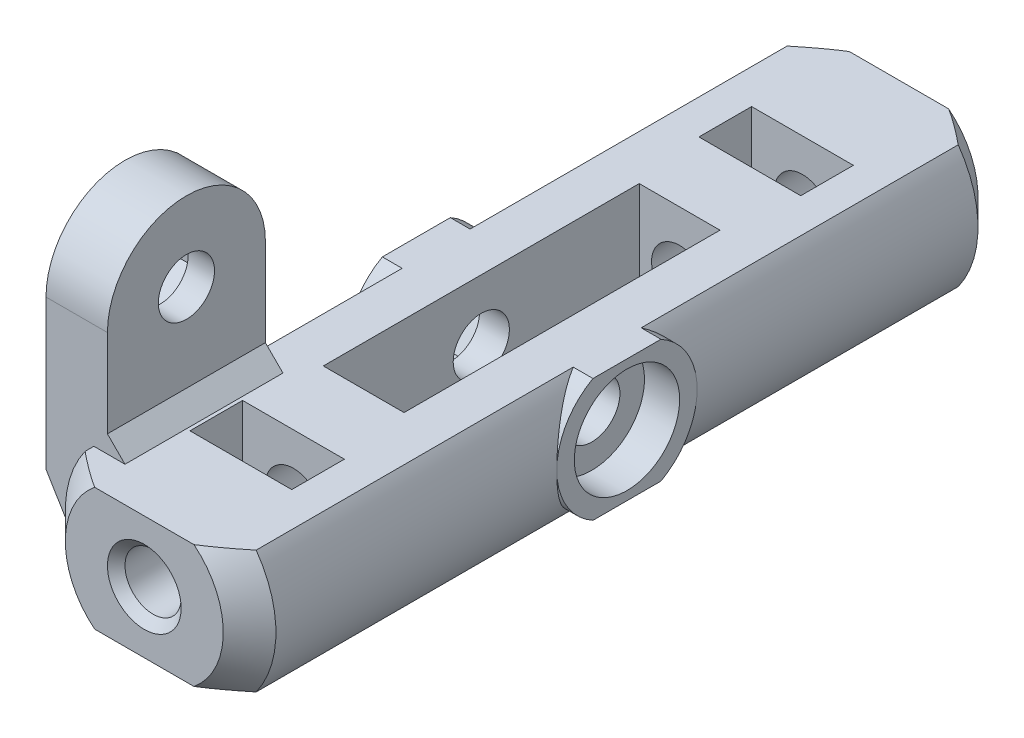
SolidWorks part; units mm, degrees
ref_plane "Front Plane" through (0, 0, 0) normal (0, 0, 1) x (1, 0, 0)
ref_plane "Top Plane" through (0, 0, 0) normal (0, 1, 0) x (1, 0, 0)
ref_plane "Right Plane" through (0, 0, 0) normal (1, 0, 0) x (0, 0, -1)
sketch "Sketch1" plane through (0, 0, 0) normal (0, 0, 1) x (1, 0, 0)
  line L0 (-4.8734, 3.5) -> (4.8734, 3.5)
  line L1 (4.8734, -3.5) -> (-4.8734, -3.5)
  arc A0 (-4.8734, 3.5) -> (-4.8734, -3.5) centre (0, 0) ccw
  arc A1 (4.8734, -3.5) -> (4.8734, 3.5) centre (0, 0) ccw
  dimension "D1" = 6
  dimension "D2" = 7
extrude "Boss-Extrude1" add sketch "Sketch1" along normal mid plane 43
sketch "Sketch5" plane through (0, 0, 0) normal (1, 0, 0) x (0, 0, -1)
  line L1 (-21.5, 3.5) -> (21.5, 3.5) construction
  line L2 (-21.5, -3.5) -> (21.5, -3.5) construction
  line L3 (-1.9365, 3.5) -> (1.9365, 3.5)
  line L4 (-1.9365, -3.5) -> (1.9365, -3.5)
  arc A0 (-1.9365, 3.5) -> (-1.9365, -3.5) centre (0, 0) ccw
  arc A1 (1.9365, -3.5) -> (1.9365, 3.5) centre (0, 0) ccw
  dimension "D1" = 8
extrude "Boss-Extrude2" add sketch "Sketch5" along normal mid plane 12
chamfer "Chamfer1" distance 1.5 angle 45 4 edges at (-6, 0, -21.5) (6, 0, -21.5) (-6, 0, 21.5) (6, 0, 21.5)
sketch "Sketch2" plane through (0, 0, 0) normal (0, 1, 0) x (1, 0, 0)
  line L1 (-2.3, 9) -> (2.3, 9)
  line L2 (-2.3, 9) -> (-2.3, -9)
  line L3 (-2.3, -9) -> (2.3, -9)
  line L4 (2.3, 9) -> (2.3, -9)
  point P4 (0, 9)
  point P6 (2.3, 0)
  dimension "D1" = 18
  dimension "D2" = 4.6
extrude "Cut-Extrude1" cut sketch "Sketch2" against normal through all and the other way through all
sketch "Sketch3" plane through (0, 0, 21.5) normal (0, 0, 1) x (1, 0, 0)
  circle A0 centre (0, 0) radius 1.6
  dimension "D1" = 3.2
extrude "Cut-Extrude2" cut sketch "Sketch3" against normal blind 16
mirror "Mirror2" about plane through (0, 0, 0) normal (0, 0, 1) of "Cut-Extrude2"
chamfer "Chamfer2" distance 0.5 angle 45 2 edges at (1.6, 0, 21.5) (1.6, 0, -21.5)
sketch "Sketch4" plane through (0, 0, 0) normal (1, 0, 0) x (0, 0, -1)
  circle A0 centre (0, 0) radius 1.6
  dimension "D1" = 3.2
extrude "Cut-Extrude3" cut sketch "Sketch4" against normal through all and the other way through all
sketch "Sketch6" plane through (6, 0, 0) normal (1, 0, 0) x (0, 0, -1)
  circle A0 centre (0, 0) radius 3
  dimension "D1" = 6
extrude "Cut-Extrude4" cut sketch "Sketch6" against normal blind 2
sketch "Sketch7" plane through (-6, 0, 0) normal (-1, 0, 0) x (0, 0, 1)
  line L1 (3.2332, 0) -> (1.6166, 2.8)
  line L2 (1.6166, 2.8) -> (-1.6166, 2.8)
  line L3 (-1.6166, 2.8) -> (-3.2332, 0)
  line L4 (-3.2332, 0) -> (-1.6166, -2.8)
  line L5 (-1.6166, -2.8) -> (1.6166, -2.8)
  line L6 (1.6166, -2.8) -> (3.2332, 0)
  circle A0 centre (0, 0) radius 2.8 construction
  dimension "D1" = 5.6
extrude "Cut-Extrude5" cut sketch "Sketch7" against normal blind 2
sketch "Sketch8" plane through (0, 0, 0) normal (1, 0, 0) x (0, 0, -1)
  line L0 (-19.5, 9.5) -> (-19.5, 1)
  line L1 (-10.5, 9.5) -> (-10.5, 1)
  line L2 (-10.5, 1) -> (-19.5, 1)
  line L4 (-20, 3.5) -> (-1.9365, 3.5) construction
  line L6 (-20, -3.5) -> (-1.9365, -3.5) construction
  arc A0 (-10.5, 9.5) -> (-19.5, 9.5) centre (-15, 9.5) ccw
  circle A1 centre (-15, 9.5) radius 1.6
  circle A3 centre (0, 0) radius 1.6 construction
  dimension "D1" = 6
  dimension "D2" = 4.5
  dimension "D3" = 15
  dimension "D4" = 9
extrude "Boss-Extrude3" add sketch "Sketch8" against normal blind 3.5 from offset 4.1 offset against normal yes
sketch "Sketch9" plane through (0, 0, 19.5) normal (0, 0, 1) x (1, 0, 0)
  line L0 (-7.6, 1) -> (-4.1, 1)
  line L1 (-4.1, 1) -> (-4.8734, -3.5)
  line L2 (-4.8734, -3.5) -> (-7.6, 1)
  line L4 (-7.6, 1) -> (-5.9161, 1) construction
  line L5 (-4.1, 9.5) -> (-4.1, 3.5) construction
extrude "Boss-Extrude4" add sketch "Sketch9" against normal up to surface (9 mm away) up to face at (-5.7221, 4.6766, 10.5)
sketch "Sketch10" plane through (0, 0, 19.5) normal (0, 0, 1) x (1, 0, 0)
  line L0 (-4.1, 4.5) -> (-3.1, 3.5)
  line L1 (-4.1, 9.5) -> (-4.1, 3.5) construction
  line L3 (-3.1, 3.5) -> (-4.1, 3.5)
  line L4 (-4.1, 3.5) -> (-4.1, 4.5)
  line L5 (4.8734, 3.5) -> (2.8284, 3.5) construction
  dimension "D1" = 1
  dimension "D2" = 1
extrude "Boss-Extrude5" add sketch "Sketch10" against normal up to surface (9 mm away) up to face at (-5.7496, 4.0614, 10.5)
sketch "Sketch11" plane through (-7.6, 0, 0) normal (-1, 0, 0) x (0, 0, 1)
  line L1 (15, 6.1514) -> (17.9, 7.8257)
  line L2 (17.9, 7.8257) -> (17.9, 11.1743)
  line L3 (17.9, 11.1743) -> (15, 12.8486)
  line L4 (15, 12.8486) -> (12.1, 11.1743)
  line L5 (12.1, 11.1743) -> (12.1, 7.8257)
  line L6 (12.1, 7.8257) -> (15, 6.1514)
  circle A0 centre (15, 9.5) radius 2.9 construction
  dimension "D1" = 5.8
extrude "Cut-Extrude6" cut sketch "Sketch11" against normal blind 2
sketch "Sketch13" plane through (0, -3.5, 0) normal (0, -1, 0) x (1, 0, 0)
  line L0 (0, 0) -> (0, 13) construction
  line L1 (-2.9, 16) -> (2.9, 16)
  line L2 (-2.9, 16) -> (-2.9, 13)
  line L3 (-2.9, 13) -> (2.9, 13)
  line L4 (2.9, 16) -> (2.9, 13)
  dimension "D1" = 5.8
  dimension "D2" = 3
  dimension "D3" = 13
extrude "Cut-Extrude8" cut sketch "Sketch13" against normal through all
mirror "Mirror4" about plane through (0, 0, 0) normal (0, 0, 1) of "Cut-Extrude8"
